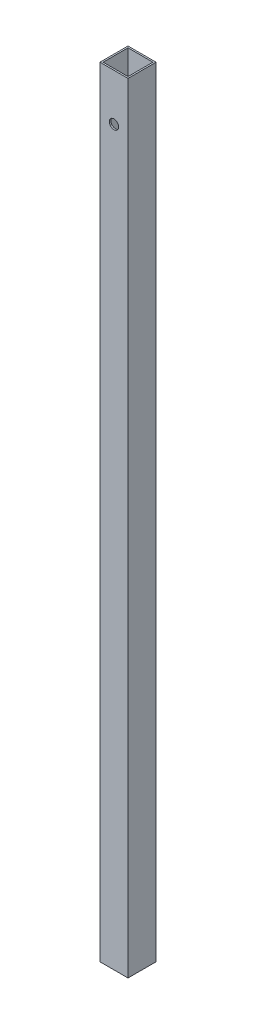
SolidWorks part; units mm, degrees
ref_plane "Front Plane" through (0, 0, 0) normal (0, 0, 1) x (1, 0, 0)
ref_plane "Top Plane" through (0, 0, 0) normal (0, 1, 0) x (1, 0, 0)
ref_plane "Right Plane" through (0, 0, 0) normal (1, 0, 0) x (0, 0, -1)
sketch "Sketch1" plane through (0, 0, 0) normal (0, 1, 0) x (1, 0, 0)
  line L0 (-8, 8) -> (-8, -8)
  line L1 (-9, 9) -> (9, 9)
  line L2 (-9, 9) -> (-9, -9)
  line L3 (-9, -9) -> (9, -9)
  line L4 (9, 9) -> (9, -9)
  line L5 (-9, 9) -> (9, -9) construction
  line L6 (-9, -9) -> (9, 9) construction
  line L7 (-8, -8) -> (8, -8)
  line L8 (8, 8) -> (8, -8)
  line L9 (-8, 8) -> (8, 8)
  point P0 (0, 0)
  dimension "D1" = 18
  dimension "D2" = 18
  dimension "D3" = 1
extrude "Boss-Extrude1" add sketch "Sketch1" along normal blind 500
sketch "Sketch2" plane through (0, 0, 9) normal (0, 0, 1) x (1, 0, 0)
  line L0 (-9, 500) -> (9, 500) construction
  line L1 (-9, 500) -> (-9, 0) construction
  circle A0 centre (0, 470) radius 3
  dimension "D1" = 6
  dimension ".5" = 30
  dimension "D3" = 9
extrude "Cut-Extrude1" cut sketch "Sketch2" against normal blind 993
